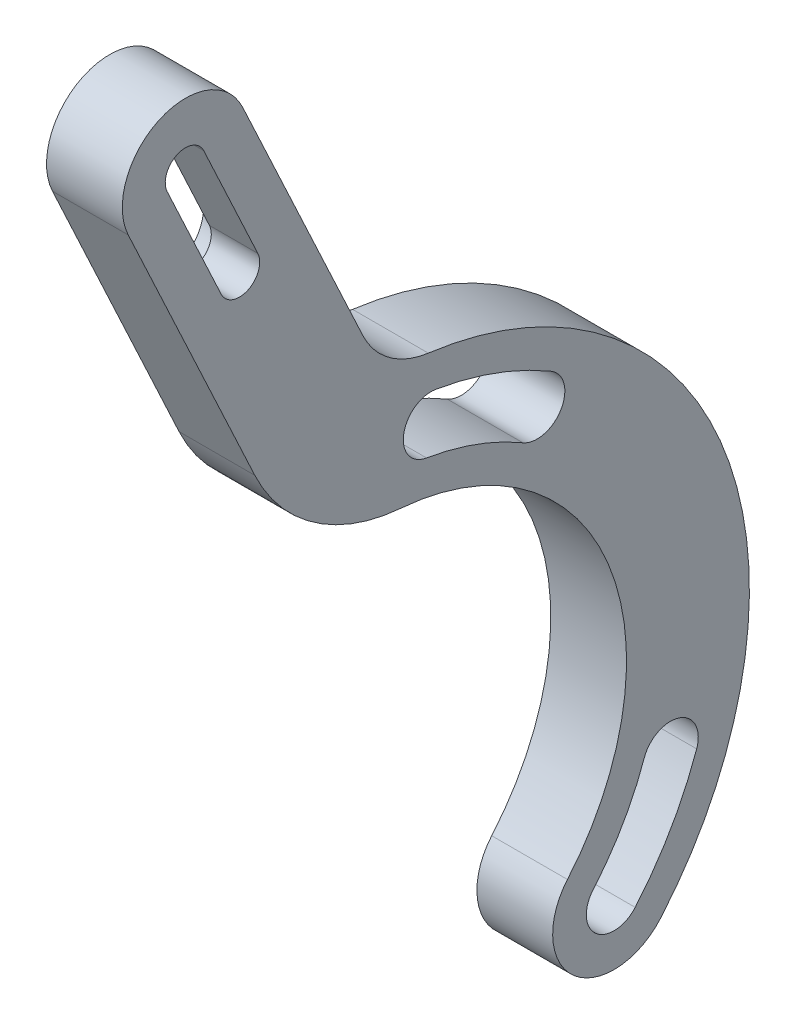
SolidWorks part; units mm, degrees
ref_plane "Front Plane" through (0, 0, 0) normal (0, 0, 1) x (1, 0, 0)
ref_plane "Top Plane" through (0, 0, 0) normal (0, 1, 0) x (1, 0, 0)
ref_plane "Right Plane" through (0, 0, 0) normal (1, 0, 0) x (0, 0, -1)
sketch "ISCG-05" plane through (0, 0, 0) normal (1, 0, 0) x (0, 0, -1)
  line L0 (0, 0) -> (12.4837, 34.2988) construction
  line L1 (0, 0) -> (-36.5, 0) construction
  line L2 (0, 0) -> (31.6099, -18.25) construction
  line L3 (0, 0) -> (-23.4617, -27.9606) construction
  line L4 (0, -64.4975) -> (0, 64.4975) construction
  line L5 (-64.4975, 0) -> (64.4975, 0) construction
  line L6 (38.0091, 164.5647) -> (346.2111, 164.5647) construction
  circle A0 centre (0, 0) radius 36.5 construction
  circle A1 centre (0, 0) radius 64.4975 construction
  point P8 (-23.4617, -27.9606)
  point P9 (31.6099, -18.25)
  point P10 (12.4837, 34.2988)
  point P11 (49.4975, 0)
  point P14 (0, -49.4975)
  dimension "D1" = 73
  dimension "D8" = 128.9949
  dimension "D2" = 100
  dimension "D3" = 100
  dimension "D4" = 50
  dimension "D5" = 15
  dimension "D6" = 15
  dimension "D7" = 70
sketch "Sketch2" plane through (0, 0, 0) normal (1, 0, 0) x (0, 0, -1)
  line L0 (0, 0) -> (-23.4617, -27.9606) construction
  line L2 (0, 0) -> (31.6099, -18.25) construction
  line L3 (0, 0) -> (12.4837, 34.2988) construction
  line L4 (31.6099, -18.25) -> (12.4837, 34.2988) construction
  line L5 (0.3549, 43.7986) -> (-16.4146, 79.7609)
  line L6 (-14.967, 41.1634) -> (-30.0092, 73.4216)
  line L7 (-26.7973, 66.5337) -> (-13.2027, 72.8729) construction
  line L8 (-18.9632, 61.8011) -> (-25.387, 75.577)
  line L9 (-14.613, 63.8296) -> (-21.0368, 77.6055)
  line L10 (-23.2119, 76.5912) -> (-16.7881, 62.8154) construction
  arc A0 (-30.7448, -25.2745) -> (-19.5517, -34.6666) centre (0, 0) ccw
  arc A1 (-25.6464, -21.0832) -> (-16.3095, -28.9178) centre (0, 0) ccw
  arc A2 (-30.7448, -25.2745) -> (-25.6464, -21.0832) centre (-28.1956, -23.1788) cw
  arc A3 (-19.5517, -34.6666) -> (-16.3095, -28.9178) centre (-17.9306, -31.7922) ccw
  arc A4 (25.2164, -21.5957) -> (30.2293, -25.8888) centre (27.7228, -23.7423) ccw
  arc A5 (31.3106, -11.0402) -> (37.535, -13.2349) centre (34.4228, -12.1375) cw
  arc A6 (5.4354, 32.752) -> (6.5159, 39.263) centre (5.9757, 36.0075) cw
  arc A7 (16.8888, 28.5833) -> (20.2463, 34.2656) centre (18.5676, 31.4244) ccw
  arc A8 (16.8888, 28.5833) -> (5.4354, 32.752) centre (0, 0) ccw
  arc A9 (20.2463, 34.2656) -> (6.5159, 39.263) centre (0, 0) ccw
  arc A10 (25.2164, -21.5957) -> (31.3106, -11.0402) centre (0, 0) ccw
  arc A11 (30.2293, -25.8888) -> (37.535, -13.2349) centre (0, 0) ccw
  circle A12 centre (0, 0) radius 36.5 construction
  circle A13 centre (0, 0) radius 29.2
  circle A14 centre (0, 0) radius 43.8
  arc A15 (-25.387, 75.577) -> (-21.0368, 77.6055) centre (-23.2119, 76.5912) cw
  arc A16 (-18.9632, 61.8011) -> (-14.613, 63.8296) centre (-16.7881, 62.8154) ccw
  arc A18 (22.1783, -18.9938) -> (33.2674, -28.4907) centre (27.7228, -23.7423) ccw
  arc A19 (-14.967, 41.1634) -> (2.3679, 29.1038) centre (4.0714, 50.0412) ccw
  arc A20 (-30.0092, 73.4216) -> (-16.4146, 79.7609) centre (-23.2119, 76.5912) cw
  point P26 (-21.3405, -25.4327)
  point P27 (28.752, -16.6)
  point P30 (11.3551, 31.1978)
  point P44 (-24.2262, 78.7664)
  point P47 (-22.1751, 68.689)
  point P50 (-17.8249, 70.7176)
  point P55 (-20, 69.7033)
  point P58 (-15.7738, 60.6402)
  dimension "D1" = 6.6
  dimension "D2" = 20
  dimension "D3" = 4
  dimension "D4" = 4
  dimension "D8" = 14.6
  dimension "D5" = 4.8
  dimension "D6" = 15
  dimension "D7" = 20
extrude "Boss-Extrude1" add sketch "Sketch2" along normal blind 9 contours A14 L5 A20 L6 A16 L8 A15 L9 | A14 A13 A11 A4 A10 A5 A9 A7 A8 A6 A3 A0 A2 A1
fillet "Fillet1" radius 10 1 edges at (4.5, 43.7986, -0.3549)
sketch "Sketch3" plane through (0, 0, 0) normal (-1, 0, 0) x (0, 0, 1)
  line L0 (18.9632, 61.8011) -> (25.387, 75.577) construction
  line L1 (14.613, 63.8296) -> (21.0368, 77.6055) construction
  line L2 (18.9632, 61.8011) -> (25.387, 75.577)
  line L3 (14.613, 63.8296) -> (21.0368, 77.6055)
  line L4 (14.967, 41.1634) -> (30.0092, 73.4216) construction
  line L5 (2.1289, 49.1251) -> (16.4146, 79.7609) construction
  line L6 (14.967, 41.1634) -> (30.0092, 73.4216)
  line L7 (2.1289, 49.1251) -> (16.4146, 79.7609)
  line L8 (-4.2747, 28.8854) -> (21.3599, 83.859) construction
  line L9 (15.695, 71.7107) -> (24.305, 67.6959) construction
  line L10 (29.9698, 79.8441) -> (8.0832, 32.9082) construction
  line L11 (24.2262, 78.7664) -> (15.7738, 60.6402) construction
  line L12 (21.0931, 60.8079) -> (27.5169, 74.5838)
  line L13 (12.4831, 64.8228) -> (18.9069, 78.5987)
  arc A0 (-5.6453, 43.4347) -> (2.1289, 49.1251) centre (-6.9342, 53.3513) ccw construction
  arc A1 (14.613, 63.8296) -> (18.9632, 61.8011) centre (16.7881, 62.8154) ccw construction
  arc A2 (25.387, 75.577) -> (21.0368, 77.6055) centre (23.2119, 76.5912) ccw construction
  arc A3 (-5.6453, 43.4347) -> (2.1289, 49.1251) centre (-6.9342, 53.3513) ccw
  arc A4 (14.613, 63.8296) -> (18.9632, 61.8011) centre (16.7881, 62.8154) ccw
  arc A5 (25.387, 75.577) -> (21.0368, 77.6055) centre (23.2119, 76.5912) ccw
  arc A6 (30.0092, 73.4216) -> (16.4146, 79.7609) centre (23.2119, 76.5912) ccw construction
  arc A7 (-2.3679, 29.1038) -> (14.967, 41.1634) centre (-4.0714, 50.0412) ccw construction
  arc A8 (30.0092, 73.4216) -> (16.4146, 79.7609) centre (23.2119, 76.5912) ccw
  arc A9 (-2.3679, 29.1038) -> (14.967, 41.1634) centre (-4.0714, 50.0412) ccw
  arc A10 (-2.3679, 29.1038) -> (-22.1783, -18.9938) centre (0, 0) ccw construction
  arc A13 (18.9069, 78.5987) -> (27.5169, 74.5838) centre (23.2119, 76.5912) cw
  arc A14 (12.4831, 64.8228) -> (21.0931, 60.8079) centre (16.7881, 62.8154) ccw
  arc A15 (27.5169, 74.5838) -> (18.9069, 78.5987) centre (23.2119, 76.5912) ccw construction
  arc A16 (12.4831, 64.8228) -> (21.0931, 60.8079) centre (16.7881, 62.8154) ccw construction
  point P17 (17.8249, 70.7176)
  point P27 (20, 69.7033)
  dimension "D1" = 9.5
extrude "Cut-Extrude1" cut sketch "Sketch3" against normal blind 3.25
